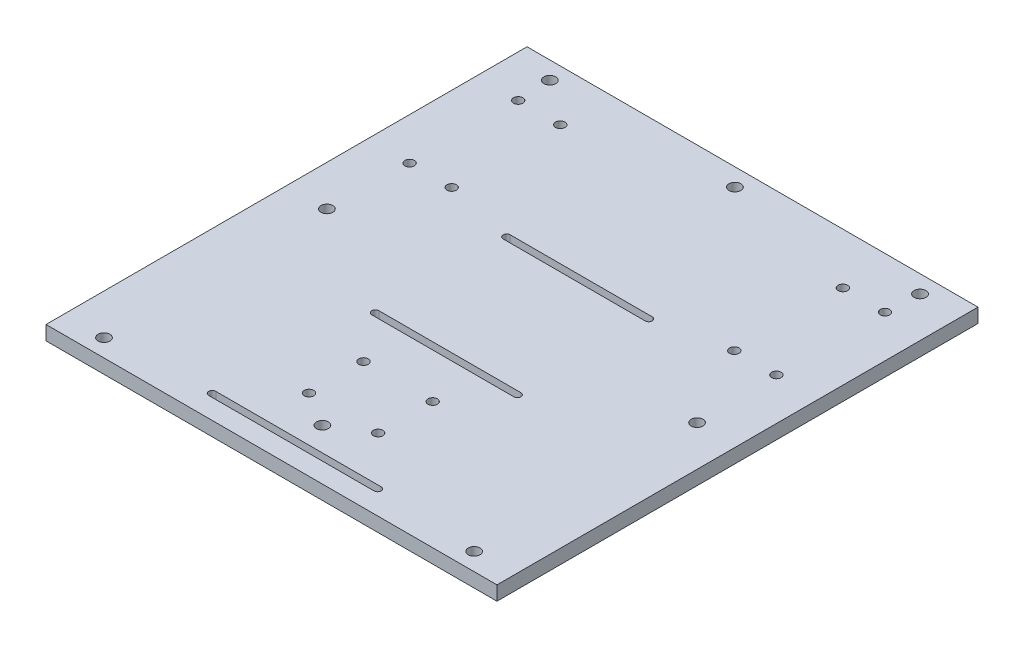
SolidWorks part; units mm, degrees
material "Acrylic (Medium-high impact)"
ref_plane "Front Plane" through (0, 0, 0) normal (0, 0, 1) x (1, 0, 0)
ref_plane "Top Plane" through (0, 0, 0) normal (0, 1, 0) x (1, 0, 0)
ref_plane "Right Plane" through (0, 0, 0) normal (1, 0, 0) x (0, 0, -1)
sketch "Sketch2" plane through (0, 0, 0) normal (0, 1, 0) x (1, 0, 0)
  line L1 (-95.25, 101.6) -> (95.25, 101.6)
  line L2 (-95.25, 101.6) -> (-95.25, -101.6)
  line L3 (-95.25, -101.6) -> (95.25, -101.6)
  line L4 (95.25, 101.6) -> (95.25, -101.6)
  line L5 (-95.25, 101.6) -> (95.25, -101.6) construction
  line L6 (-95.25, -101.6) -> (95.25, 101.6) construction
  point P0 (0, 0)
extrude "Boss-Extrude1" add sketch "Sketch2" along normal blind 6
sketch "Sketch3" plane through (0, 6, 0) normal (0, 1, 0) x (1, 0, 0)
  line L0 (0, 101.6) -> (0, -101.6) construction
  line L1 (95.25, 101.6) -> (-95.25, 101.6) construction
  line L2 (-95.25, -101.6) -> (95.25, -101.6) construction
  line L3 (-95.25, 0) -> (-77.47, 0)
  line L4 (-95.25, 101.6) -> (-95.25, -101.6) construction
  line L5 (-95.25, 0) -> (95.25, 0) construction
  line L6 (95.25, -101.6) -> (95.25, 101.6) construction
  line L7 (-77.47, 46.1542) -> (-77.47, -46.1542)
  line L8 (-77.47, 46.1542) -> (-77.47, 68.15)
  line L9 (-77.47, 68.15) -> (-77.47, 80.088)
  line L10 (-77.47, 68.15) -> (-59.69, 68.15)
  circle A0 centre (-77.47, 34.2162) radius 2
  circle A1 centre (-77.47, 80.088) radius 2
  circle A6 centre (77.47, 34.2162) radius 2
  circle A7 centre (77.47, 80.088) radius 2
  circle A8 centre (-59.69, 80.088) radius 2
  circle A9 centre (-59.69, 34.2162) radius 2
  circle A14 centre (59.69, 80.088) radius 2
  circle A15 centre (59.69, 34.2162) radius 2
  point P16 (-77.47, 0)
  point P17 (-77.47, 0)
  dimension "D1" = 11.938
  dimension "D2" = 21.9958
extrude "Cut-Extrude2" cut sketch "Sketch3" against normal blind 6
sketch "Sketch4" plane through (0, 6, 0) normal (0, 1, 0) x (1, 0, 0)
  line L0 (0, 101.6) -> (0, -101.6) construction
  line L1 (-95.25, -101.6) -> (95.25, -101.6) construction
  line L2 (-95.25, 0) -> (95.25, 0) construction
  line L3 (95.25, -101.6) -> (95.25, 101.6) construction
  line L4 (0, -101.6) -> (0, -91.6994)
  line L6 (-34.925, -90.1994) -> (34.925, -90.1994)
  line L7 (-34.925, -93.1994) -> (34.925, -93.1994)
  arc A0 (-34.925, -90.1994) -> (-34.925, -93.1994) centre (-34.925, -91.6994) ccw
  arc A1 (34.925, -93.1994) -> (34.925, -90.1994) centre (34.925, -91.6994) ccw
  point P6 (0, 0)
  point P12 (0, 0)
  point P16 (0, -91.6994)
  dimension "D1" = 1.5
extrude "Cut-Extrude3" cut sketch "Sketch4" against normal through all
sketch "Sketch5" plane through (0, 6, 0) normal (0, 1, 0) x (1, 0, 0)
  line L0 (-78.187, 101.6) -> (-78.187, 86.7301)
  line L1 (95.25, 101.6) -> (-95.25, 101.6) construction
  line L2 (-78.187, 94.1651) -> (-95.25, 94.1651)
  line L3 (-95.25, 101.6) -> (-95.25, -101.6) construction
  line L4 (0, 101.6) -> (0, -101.6)
  line L5 (-95.25, -101.6) -> (95.25, -101.6) construction
  line L6 (0, 0) -> (-95.25, 0)
  line L7 (0, 0) -> (95.25, 0)
  line L8 (95.25, -101.6) -> (95.25, 101.6) construction
  circle A0 centre (-78.187, 94.1651) radius 2.5
  circle A1 centre (78.187, 94.1651) radius 2.5
  circle A2 centre (-78.187, -94.1651) radius 2.5
  circle A3 centre (78.187, -94.1651) radius 2.5
  circle A4 centre (-78.187, 0) radius 2.5
  circle A5 centre (78.187, 0) radius 2.5
  circle A7 centre (0, 94.1651) radius 2.5
  circle A9 centre (0, -80.088) radius 2.5
extrude "Cut-Extrude6" cut sketch "Sketch5" against normal through all
sketch "Sketch8" plane through (0, 6, 0) normal (0, 1, 0) x (1, 0, 0)
  line L0 (-30, 29.25) -> (30, 29.25)
  line L2 (-30, 26.25) -> (-30, -26.25)
  line L4 (30, 27.75) -> (30, -26.25)
  line L5 (-30, 27.75) -> (-28.8989, 26.7314) construction
  line L6 (-28.8989, -26.7314) -> (28.3784, 26.25) construction
  line L7 (-30, 26.25) -> (30, 26.25)
  line L8 (-30, -26.25) -> (30, -26.25)
  line L9 (-30, -29.25) -> (30, -29.25)
  line L10 (-28.3784, 26.25) -> (28.3784, -26.25) construction
  arc A0 (-30, 29.25) -> (-30, 26.25) centre (-30, 27.75) ccw
  arc A1 (30, 26.25) -> (30, 29.25) centre (30, 27.75) ccw
  arc A2 (-30, -26.25) -> (-30, -29.25) centre (-30, -27.75) ccw
  arc A3 (30, -29.25) -> (30, -26.25) centre (30, -27.75) ccw
  point P0 (0, 0)
extrude "Cut-Extrude12" cut sketch "Sketch8" against normal blind 10
sketch "Sketch9" plane through (0, 6, 0) normal (0, 1, 0) x (1, 0, 0)
  line L0 (0, -101.6) -> (0, 101.6)
  line L1 (-95.25, -101.6) -> (95.25, -101.6) construction
  line L2 (95.25, 101.6) -> (-95.25, 101.6) construction
  line L4 (-14.61, -48.1124) -> (14.61, -48.1124)
  line L5 (-14.61, -48.1124) -> (-14.61, -71.1524)
  line L6 (-14.61, -71.1524) -> (14.61, -71.1524)
  line L7 (14.61, -48.1124) -> (14.61, -71.1524)
  line L8 (-14.61, -48.1124) -> (14.61, -71.1524) construction
  line L9 (-14.61, -71.1524) -> (14.61, -48.1124) construction
  circle A0 centre (-14.61, -48.1124) radius 2
  circle A1 centre (14.61, -48.1124) radius 2
  circle A2 centre (14.61, -71.1524) radius 2
  circle A3 centre (-14.61, -71.1524) radius 2
  point P6 (0, -59.6324)
extrude "Cut-Extrude13" cut sketch "Sketch9" against normal through all contours L5 A3 L6 | L6 A3 L5 | L7 A2 L6 | L6 A2 L7 | L7 A1 L4 | L4 A1 L7 | L5 A0 L4 | L4 A0 L5
